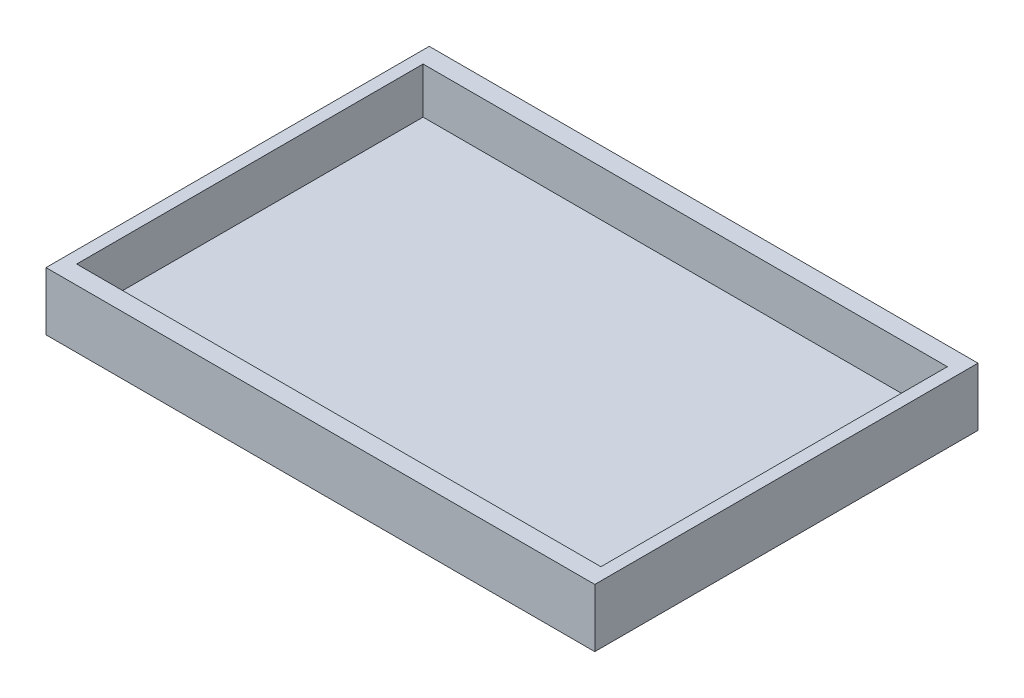
SolidWorks part; units mm, degrees
ref_plane "Front Plane" through (0, 0, 0) normal (0, 0, 1) x (1, 0, 0)
ref_plane "Top Plane" through (0, 0, 0) normal (0, 1, 0) x (1, 0, 0)
ref_plane "Right Plane" through (0, 0, 0) normal (1, 0, 0) x (0, 0, -1)
sketch "Sketch1" plane through (0, 0, 0) normal (0, 1, 0) x (1, 0, 0)
  line L1 (-44.75, 31.25) -> (44.75, 31.25)
  line L2 (-44.75, 31.25) -> (-44.75, -31.25)
  line L3 (-44.75, -31.25) -> (44.75, -31.25)
  line L4 (44.75, 31.25) -> (44.75, -31.25)
  line L5 (-44.75, 31.25) -> (44.75, -31.25) construction
  line L6 (-44.75, -31.25) -> (44.75, 31.25) construction
  point P0 (0, 0)
  dimension "D1" = 89.5
  dimension "D2" = 62.5
extrude "Boss-Extrude1" add sketch "Sketch1" along normal blind 2
sketch "Sketch7" plane through (0, 2, 0) normal (0, 1, 0) x (1, 0, 0)
  line L2 (-42.5, -28) -> (-42.5, -31.25) construction
  line L3 (-42.75, 28.25) -> (-42.75, -28.25)
  line L8 (-42.75, -28.25) -> (42.75, -28.25)
  line L9 (42.75, 28.25) -> (42.75, -28.25)
  line L10 (-42.75, 28.25) -> (42.75, 28.25)
  line L13 (-42.5, 28) -> (42.5, 28)
  line L14 (-42.5, 28) -> (-42.5, -28)
  line L15 (-42.5, -28) -> (42.5, -28)
  line L24 (44.75, -31.25) -> (44.75, 31.25)
  line L25 (44.75, 31.25) -> (-44.75, 31.25)
  line L26 (-44.75, 31.25) -> (-44.75, -31.25)
  line L27 (-44.75, -31.25) -> (44.75, -31.25)
  line L28 (44.75, -31.25) -> (44.75, 31.25)
  line L29 (44.75, 31.25) -> (-44.75, 31.25)
  line L30 (-44.75, 31.25) -> (-44.75, -31.25)
  line L31 (-44.75, -31.25) -> (44.75, -31.25)
  line L32 (42.5, 28) -> (42.5, -28)
  dimension "D2" = 3
  dimension "D3" = 2
  dimension "D5" = 2
  dimension "D6" = 3
  dimension "D7" = 85
  dimension "D8" = 56
  dimension "D4" = 0.25
extrude "Boss-Extrude5" add sketch "Sketch7" along normal blind 7.5
equation "\"USBC_Width\"= 9mm"
equation "\"USBC_Height\"= 3.2m"
equation "\"MicroHDMI_Width\"= 6.5mm"
equation "\"MicroHDMI_Height\"= 3mm"
equation "\"RPI_Width\"= 56mm"
equation "\"RPI_Length\"= 85mm"
equation "\"AudioJack_Diameter\"= 6mm"
equation "\"AudioJack_Height\"= 6mm"
equation "\"USB2_Width\"= 13.15mm"
equation "\"USB2_Height\"= 16mm"
equation "\"USB3_Width\"= 13.15mm"
equation "\"USB3_Height\"= 16mm"
equation "\"RJ45_Width\"= 16mm"
equation "\"RJ45_Height\"= 13.5mm"
equation "\"GPIO_Height\"= 8.5mm"
equation "\"D1@Sketch1\"=\"RPI_Length\"+\"SDCard_Side_Case_Thickness\"+\"RJ45_Side_Case_Thickness\"+\"RPIEdgeToCaseWall_Tolerance\"*2"
equation "\"D2@Sketch1\"=\"RPI_Width\"+\"CaseWallThickness\"+\"RPIEdgeToCaseWall_Tolerance\"*2+\"Power_Connector_Side_Case_Thickness\""
equation "\"Connector_Width_Tolerance\"= .25mm"
equation "\"RPI_Standoff_Height\"= 3mm"
equation "\"RPI_Board_Thickness\"= 1.5mm"
equation "\"D1@Boss-Extrude3\"=\"RPI_Standoff_Height\""
equation "\"D1@Boss-Extrude5\"=\"RPI_Standoff_Height\"+\"RPI_Board_Thickness\"+(\"AudioJack_Diameter\"/2)"
equation "\"RPI_Corner_Radius\"= 3mm"
equation "\"D2@Sketch9\"=\"RPI_Board_Thickness\""
equation "\"D3@Sketch9\"=\"USBC_Width\"+\"Connector_Width_Tolerance\""
equation "\"D5@Sketch9\"=\"MicroHDMI_Width\"+\"Connector_Width_Tolerance\""
equation "\"D6@Sketch9\"=\"MicroHDMI_Width\"+\"Connector_Width_Tolerance\""
equation "\"USBC_Receptacle_Radius\"= 1.28mm"
equation "\"D1@Fillet2\"=\"USBC_Receptacle_Radius\""
equation "\"MicroHDMI_Chamfer_HorizontalLength\"= 1mm"
equation "\"D3@Chamfer1\"=\"MicroHDMI_Chamfer_HorizontalLength\""
equation "\"D1@Chamfer1\"=\"MicroHDMI_Chamfer_VerticalLength\""
equation "\"MicroHDMI_Chamfer_VerticalLength\"= 1mm"
equation "\"D7@Sketch9\"=\"AudioJack_Diameter\"+\"Connector_Width_Tolerance\""
equation "\"USBToRPI_Gap\"= 1.3mm"
equation "\"D1@Sketch10\"=\"RPI_Board_Thickness\"+\"USBToRPI_Gap\""
equation "\"D2@Sketch10\"=\"USB2_Width\"+\"Connector_Width_Tolerance\""
equation "\"D7@Sketch10\"=\"USB3_Width\"+\"Connector_Width_Tolerance\""
equation "\"D8@Sketch10\"=\"RJ45_Width\"+\"Connector_Width_Tolerance\""
equation "\"RPIEdgeToCaseWall_Tolerance\"= .25mm"
equation "\"D4@Sketch7\"=\"RPIEdgeToCaseWall_Tolerance\""
equation "\"MicroSDSlot_Width\"= 12mm"
equation "\"MiroSDSlot_Thickness\"= 1mm"
equation "\"D5@Sketch11\"=\"RPI_Width\""
equation "\"D6@Sketch11\"=\"MicroSDSlot_Width\"/2+22mm"
equation "\"CaseWallThickness\"= 3mm"
equation "\"D1@Cut-Extrude4\"=\"CaseWallThickness\"+\"RPIEdgeToCaseWall_Tolerance\"+7mm"
equation "\"D1@Boss-Extrude6\"=\"RPI_Standoff_Height\""
equation "\"D1@Boss-Extrude7\"=\"RPI_Standoff_Height\"-1.5mm"
equation "\"D7@Sketch11\"=\"RPI_Standoff_Height\"+\"CaseFloorThickness\""
equation "\"CaseFloorThickness\"= 2mm"
equation "\"D1@Boss-Extrude4\"=\"RPI_Board_Thickness\"+.5mm"
equation "\"D9@Sketch10\"=\"RPI_Board_Thickness\""
equation "\"RJ45ToRPI_Gap\"= .3mm"
equation "\"Power_Connector_Side_Case_Thickness\"= 3mm"
equation "\"D2@Sketch7\"=\"CaseWallThickness\""
equation "\"D6@Sketch7\"=\"Power_Connector_Side_Case_Thickness\""
equation "\"D1@Sketch2\"=\"RPI_Width\""
equation "\"D3@Sketch2\"=\"RPI_Length\""
equation "\"D6@Sketch10\"=\"RPIEdgeToCaseWall_Tolerance\""
equation "\"D2@Sketch15\"=\"RPIEdgeToCaseWall_Tolerance\"+7.9"
equation "\"D6@Sketch15\"=\"RPI_Board_Thickness\""
equation "\"SDCard_Side_Case_Thickness\"= 2mm"
equation "\"RJ45_Side_Case_Thickness\"= 2mm"
equation "\"D3@Sketch7\"=\"SDCard_Side_Case_Thickness\""
equation "\"D5@Sketch7\"=\"RJ45_Side_Case_Thickness\""
